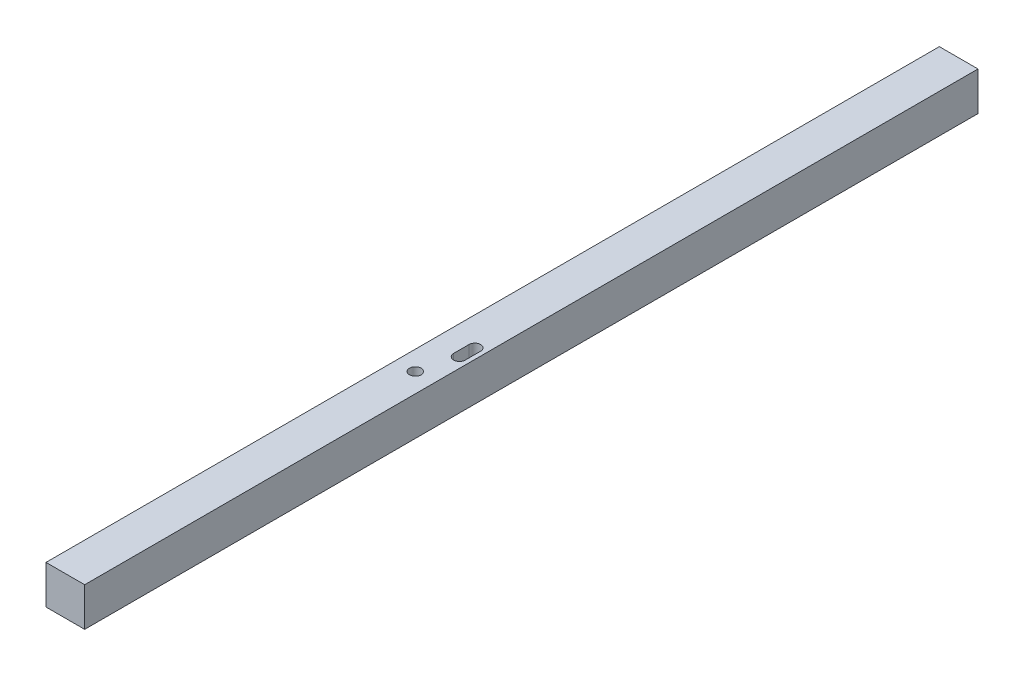
SolidWorks part; units mm, degrees
ref_plane "Plan de face" through (0, 0, 0) normal (0, 0, 1) x (1, 0, 0)
ref_plane "Plan de dessus" through (0, 0, 0) normal (0, 1, 0) x (1, 0, 0)
ref_plane "Plan de droite" through (0, 0, 0) normal (1, 0, 0) x (0, 0, -1)
sketch "Esquisse1" plane through (0, 0, 0) normal (0, 0, 1) x (1, 0, 0)
  line L0 (-5, 5) -> (5, -5) construction
  line L1 (-5, 5) -> (5, 5)
  line L2 (-5, 5) -> (-5, -5)
  line L3 (-5, -5) -> (5, -5)
  line L4 (5, 5) -> (5, -5)
  dimension "D1" = 10
extrude "Boss.-Extru.1" add sketch "Esquisse1" along normal offset from surface 2 and the other way offset from surface (115.5 mm away) 2
sketch "Esquisse2" plane through (0, -5, 0) normal (0, -1, 0) x (1, 0, 0)
  circle A0 centre (0, 25) radius 1.5 construction
  circle A2 centre (0, 25) radius 1.5
extrude "Enlèv. mat.-Extru.1" cut sketch "Esquisse2" against normal through all
sketch "Esquisse3" plane through (0, -5, 0) normal (0, -1, 0) x (1, 0, 0)
  line L0 (2.4, 12) -> (2.4, 16) construction
  line L1 (0.9, 12) -> (0.9, 16)
  line L2 (3.9, 12) -> (3.9, 16)
  arc A0 (0.9, 12) -> (3.9, 12) centre (2.4, 12) ccw
  arc A1 (3.9, 16) -> (0.9, 16) centre (2.4, 16) ccw
  arc A2 (0.4, 12) -> (4.4, 12) centre (2.4, 12) ccw construction
  arc A3 (4.4, 16) -> (0.4, 16) centre (2.4, 16) ccw construction
  point P2 (2.4, 14)
  dimension "D1" = 3
extrude "Enlèv. mat.-Extru.2" cut sketch "Esquisse3" against normal through all
